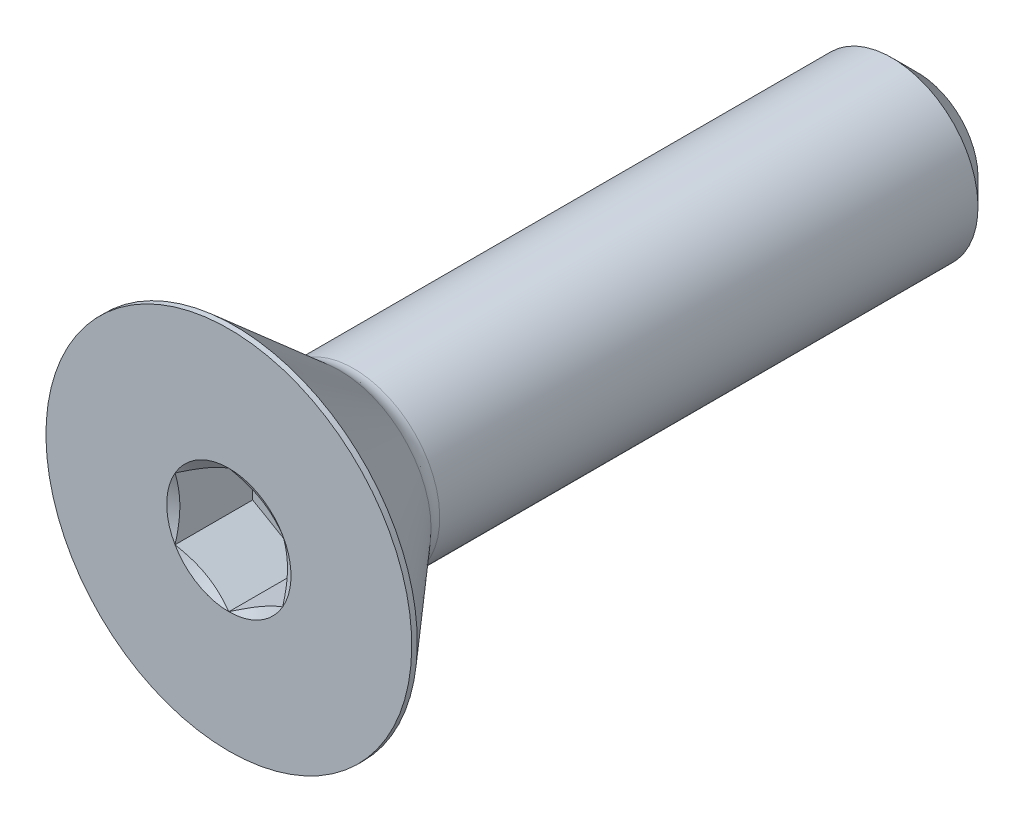
SolidWorks part; units mm, degrees
material "Alloy Steel"
ref_plane "Front" through (0, 0, 0) normal (0, 0, 1) x (1, 0, 0)
ref_plane "Top" through (0, 0, 0) normal (0, 1, 0) x (1, 0, 0)
ref_plane "Right" through (0, 0, 0) normal (1, 0, 0) x (0, 0, -1)
sketch "Sketch1" plane through (0, 0, 0) normal (1, 0, 0) x (0, 0, -1)
  line L0 (0, 6.7437) -> (0.2045, 6.7437) construction
  line L1 (0.2045, 6.7437) -> (4.0894, 3.3666) construction
  line L2 (0, 3.175) -> (25.4, 3.175)
  line L3 (25.4, 3.175) -> (25.4, 0)
  line L4 (25.4, 0) -> (0, 0)
  line L5 (0, 0) -> (0, 6.7437) construction
  line L6 (0, 6.7437) -> (0, -6.7437) construction
  line L7 (25.4, 3.175) -> (25.4, -3.175) construction
  line L8 (0, -6.7437) -> (0.2045, -6.7437) construction
  line L9 (0.2045, -6.7437) -> (4.0894, -3.3666) construction
  line L11 (0, 3.175) -> (0, 0)
  line L12 (4.6018, 3.175) -> (4.6018, 0) construction
  line L13 (0, 0) -> (0, 3.175) construction
  arc A1 (4.0894, 3.3666) -> (4.6018, 3.175) centre (4.6018, 3.956) ccw construction
  dimension "D1" = 0.2045
  dimension "Min Thread" = 25.4
revolve "Revolve1" add sketch "Sketch1" angle 360 mid plane about L4
cosmetic thread "Cosmetic Thread3" parameters "D2"=4.8387
sketch "Sketch3" plane through (0, 0, -25.4) normal (0, 0, -1) x (-1, 0, 0)
  circle A0 centre (0, 0) radius 3.175
curve "Helix/Spiral1" pitch 1.27 height 25.4 turns 20
sketch "Sketch2" plane through (0, 0, 0) normal (1, 0, 0) x (0, 0, -1)
  line L0 (25.4, 3.175) -> (26.5113, 3.175)
  line L1 (26.5113, 3.175) -> (26.035, 2.3501)
  line L2 (26.035, 2.3501) -> (25.8762, 2.3501)
  line L3 (25.8762, 2.3501) -> (25.4, 3.175)
  line L4 (25.6381, 2.7626) -> (26.2731, 2.7626) construction
  dimension "D1" = 60
  dimension "D2" = 0.1588
  dimension "D3" = 0.635
ref_plane "Plane2" [suppressed] through (0, 0, 15.875) normal (0, 0, 1) x (1, 0, 0)
chamfer "Chamfer1" distance 0.9525 angle 45 1 edges at (0, 3.175, -25.4)
sketch "Sketch7" plane through (0, 0, 0) normal (1, 0, 0) x (0, 0, -1)
  line L0 (0, 6.7437) -> (0.2045, 6.7437) construction
  line L1 (0.2045, 6.7437) -> (4.0894, 3.3666) construction
  line L2 (0, 6.7437) -> (0.2045, 6.7437)
  line L3 (0.2045, 6.7437) -> (4.0894, 3.3666)
  line L4 (4.6018, 3.175) -> (4.6018, 0) construction
  line L5 (4.6018, 3.175) -> (4.6018, 0)
  line L7 (0, 0) -> (0, 6.7437) construction
  line L8 (0, 0) -> (0, 6.7437)
  line L9 (0, 0) -> (4.6018, 0)
  line L10 (5.7417, 0) -> (-5.7417, 0) construction
  arc A0 (4.0894, 3.3666) -> (4.6018, 3.175) centre (4.6018, 3.956) ccw construction
  arc A1 (4.0894, 3.3666) -> (4.6018, 3.175) centre (4.6018, 3.956) ccw
revolve "Revolve2" add sketch "Sketch7" angle 360 mid plane about L9
ref_plane "Plane1" through (0, 0, -4.6018) normal (0, 0, 1) x (1, 0, 0)
sketch "Sketch8" plane through (0, 0, -4.6018) normal (0, 0, 1) x (1, 0, 0)
  circle A0 centre (0, 0) radius 3.175
extrude "Boss-Extrude1" add sketch "Sketch8" against normal through all draft 46
sketch "Sketch5" plane through (0, 0, 0) normal (0, 0, 1) x (1, 0, 0)
  line L0 (0, 0) -> (-2.2914, 0) construction
  line L1 (0, 0) -> (-2.7496, 1.5875) construction
  line L2 (0, 0) -> (-2.7496, -1.5875) construction
  line L6 (0, 2.2914) -> (0, 1.8898) construction
  line L7 (0, 1.8898) -> (0, 1.4883) construction
  line L9 (0, 2.2914) -> (-1.9844, 1.1457)
  line L10 (-1.9844, 1.1457) -> (-1.9844, -1.1457)
  line L11 (-1.9844, -1.1457) -> (0, -2.2914)
  line L12 (0, -2.2914) -> (1.9844, -1.1457)
  line L13 (1.9844, -1.1457) -> (1.9844, 1.1457)
  line L14 (1.9844, 1.1457) -> (0, 2.2914)
  circle A0 centre (0, 0) radius 2.2914 construction
  circle A1 centre (0, 0) radius 1.8898 construction
  circle A2 centre (0, 0) radius 1.4883 construction
  circle A3 centre (0, 0) radius 1.9844 construction
  dimension "D3" = 2.9766
  dimension "D4" = 30
  dimension "D5" = 30
  dimension "Hex" = 3.9688
extrude "Cut-Extrude2" cut sketch "Sketch5" against normal blind 2.8626
sketch "Sketch6" plane through (0, 0, 0) normal (0, 0, 1) x (1, 0, 0)
  circle A0 centre (0, 0) radius 2.2914
extrude "Cut-Extrude3" cut sketch "Sketch6" against normal blind 2.8626 draft 60
sketch "Sketch9" [suppressed] plane through (0, 0, -3.6076) normal (0, 0, 1) x (1, 0, 0)
  circle A1 centre (0, 0) radius 2.413
  circle A2 centre (0, 0) radius 2.413
  point P0 (0, 2.413)
  dimension "D1" = 0
extrude "Boss-Extrude2" [suppressed] add sketch "Sketch9" against normal up to surface (15.4424 mm away)
sketch "Sketch10" plane through (0, 0, 0) normal (1, 0, 0) x (0, 0, -1)
  line L0 (25.4, 3.175) -> (25.4, -3.175) construction
  point P0 (23.495, -3.175)
  dimension "D1" = 1.905
equation "\"D3@Helix/Spiral1\" = \"Lg@Sketch1\""
equation "\"D2@Sketch2\" = \"D4@Helix/Spiral1\" * .125"
equation "\"D3@Sketch2\" = \"D4@Helix/Spiral1\" * .5"
equation "\"D1@Chamfer1\" = \"D4@Helix/Spiral1\" * .75"
equation "\"D1@Cut-Extrude2\" = \"Head Ht@Sketch1\" * .7"
equation "\"D1@Sketch1\" = \"Head Ht@Sketch1\" * .05"
equation "\"D1@Sketch10\" = \"D4@Helix/Spiral1\" * 1.5"
equation "\"D1@Cut-Extrude3\"= \"D1@Cut-Extrude2\""
equation "\"D3@Sketch5\" = \"Hex@Sketch5\" * .75"
